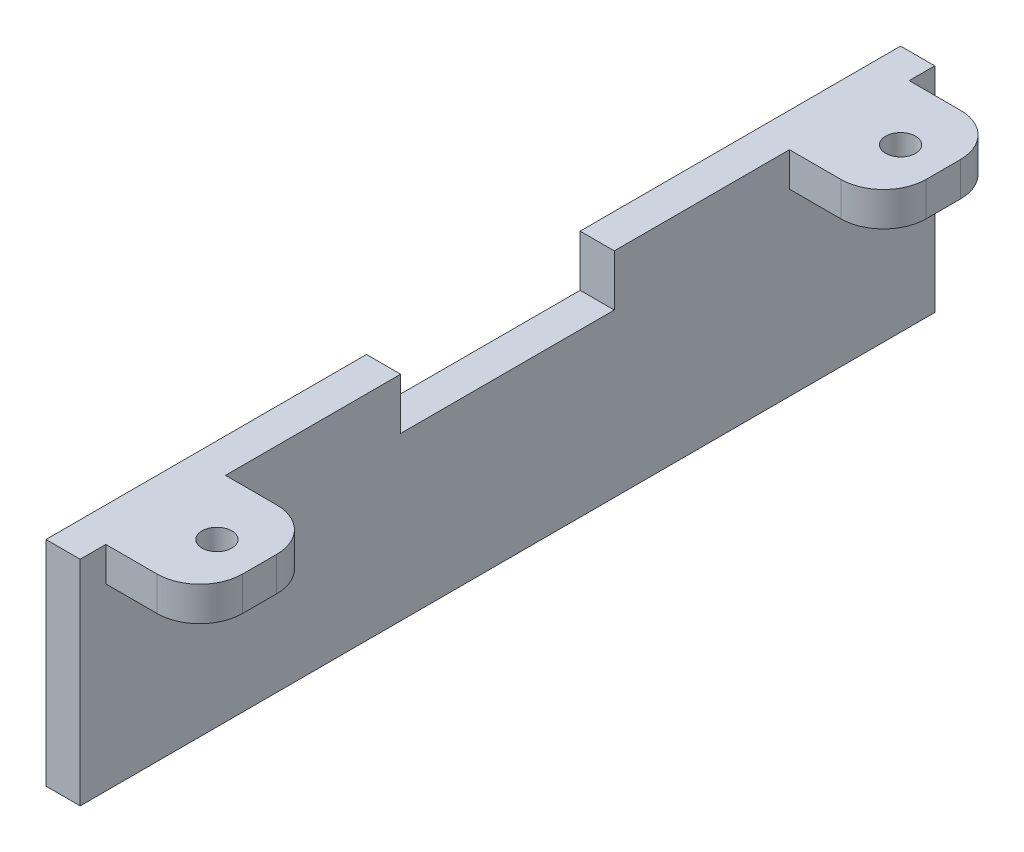
SolidWorks part; units mm, degrees
ref_plane "Plano frontal" through (0, 0, 0) normal (0, 0, 1) x (1, 0, 0)
ref_plane "Plano superior" through (0, 0, 0) normal (0, 1, 0) x (1, 0, 0)
ref_plane "Plano direito" through (0, 0, 0) normal (1, 0, 0) x (0, 0, -1)
sketch "Esboço1" plane through (0, 0, 0) normal (0, 0, 1) x (1, 0, 0)
  line L0 (15, 0) -> (0, 0)
  line L1 (0, 0) -> (0, -25)
  line L2 (0, -25) -> (4, -25)
  line L3 (4, -25) -> (4, -4)
  line L4 (4, -4) -> (15, -4)
  line L5 (15, -4) -> (15, 0)
  dimension "D1" = 15
  dimension "D2" = 4
  dimension "D3" = 4
  dimension "D4" = 25
extrude "Ressalto-extrusão1" add sketch "Esboço1" along normal blind 100
sketch "Esboço2" plane through (0, 0, 0) normal (0, 1, 0) x (1, 0, 0)
  line L0 (15, 0) -> (15, -3)
  line L1 (15, -50) -> (3.4766, -50) construction
  line L2 (15, -100) -> (15, 0) construction
  line L3 (4, -100) -> (4, 0) construction
  line L4 (15, -17) -> (4, -17)
  line L5 (15, -83) -> (4, -83)
  line L6 (15, -17) -> (15, -83)
  line L7 (4, -17) -> (4, -83)
  line L8 (15, -50) -> (4, -50) construction
  line L9 (9.5, -10) -> (15, -10) construction
  line L10 (4, -100) -> (15, -100)
  line L11 (4, -100) -> (4, -97)
  line L12 (4, -97) -> (15, -97)
  line L13 (15, -100) -> (15, -97)
  line L14 (4, -3) -> (15, -3)
  line L15 (4, 0) -> (4, -3)
  line L16 (4, 0) -> (15, 0)
  line L19 (4, -100) -> (4, 0) construction
  line L20 (4, -90) -> (15, -90) construction
  line L21 (15, -100) -> (15, 0) construction
  circle A0 centre (10, -10) radius 1.75
  circle A1 centre (10, -90) radius 1.75
  dimension "D2" = 3.5
  dimension "D1" = 80
  dimension "D5" = 5
  dimension "D3" = 7
extrude "Corte-extrusão1" cut sketch "Esboço2" against normal blind 100
fillet "Filete1" radius 5 4 edges at (15, -2, 83) (15, -2, 17) (15, -2, 97) (15, -2, 3)
sketch "Esboço3" plane through (0, 0, 0) normal (-1, 0, 0) x (0, 0, 1)
  line L0 (100, 0) -> (0, 0) construction
  line L1 (37.5, 6) -> (62.5, 6)
  line L2 (37.5, 6) -> (37.5, -6)
  line L3 (37.5, -6) -> (62.5, -6)
  line L4 (62.5, 6) -> (62.5, -6)
  line L5 (37.5, 6) -> (62.5, -6) construction
  line L6 (37.5, -6) -> (62.5, 6) construction
  point P0 (50, 0)
  dimension "D1" = 25
  dimension "D2" = 6
extrude "Corte-extrusão2" cut sketch "Esboço3" against normal blind 100
